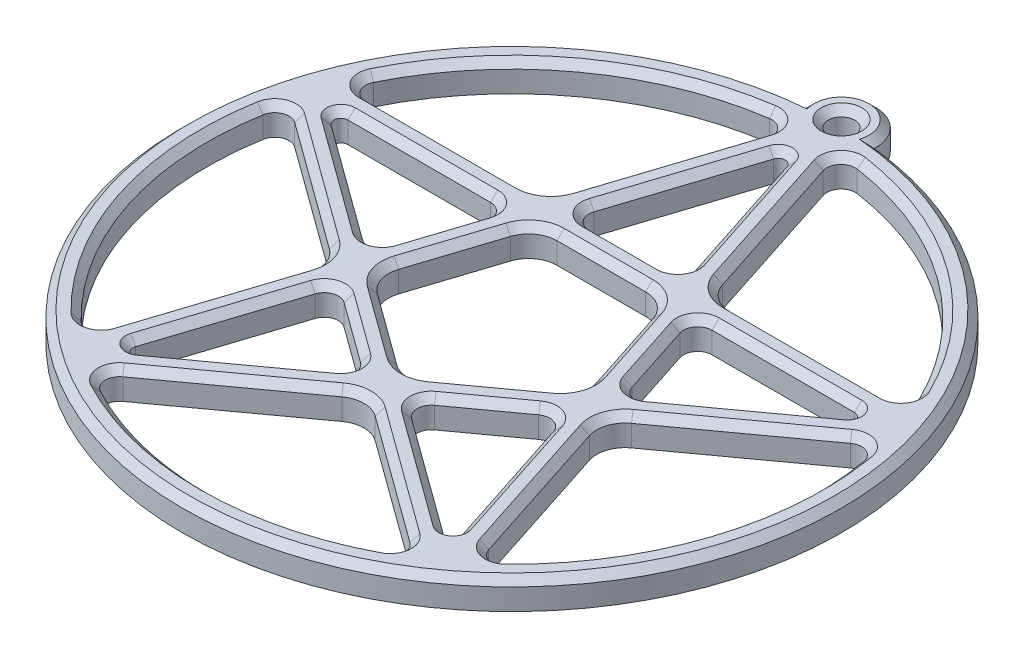
SolidWorks part; units mm, degrees
ref_plane "Front Plane" through (0, 0, 0) normal (0, 0, 1) x (1, 0, 0)
ref_plane "Top Plane" through (0, 0, 0) normal (0, 1, 0) x (1, 0, 0)
ref_plane "Right Plane" through (0, 0, 0) normal (1, 0, 0) x (0, 0, -1)
sketch "Sketch1" plane through (0, 0, 0) normal (0, 1, 0) x (1, 0, 0)
  line L0 (-44.0839, 14.3237) -> (44.0839, 14.3237) construction
  line L1 (44.0839, 14.3237) -> (0, 46.3525) construction
  line L2 (0, 46.3525) -> (-44.0839, 14.3237) construction
  line L3 (-44.0839, 14.3237) -> (-27.2453, -37.5) construction
  line L4 (-27.2453, -37.5) -> (27.2453, -37.5) construction
  line L5 (27.2453, -37.5) -> (44.0839, 14.3237) construction
  line L6 (44.0839, 14.3237) -> (-27.2453, -37.5) construction
  line L7 (-27.2453, -37.5) -> (0, 46.3525) construction
  line L8 (0, 46.3525) -> (27.2453, -37.5) construction
  line L9 (27.2453, -37.5) -> (-44.0839, 14.3237) construction
  line L10 (-43.4764, 16.0737) -> (43.4764, 16.0737) construction
  line L11 (-44.6146, 12.5737) -> (44.6146, 12.5737) construction
  line L12 (-1.8521, 46.3155) -> (-28.722, -36.3814) construction
  line L13 (1.8283, 46.3165) -> (-25.745, -38.5455) construction
  line L14 (-1.8283, 46.3165) -> (25.745, -38.5455) construction
  line L15 (1.8521, 46.3155) -> (28.722, -36.3814) construction
  line L16 (-43.4846, 16.0514) -> (28.7033, -36.3961) construction
  line L17 (-44.621, 12.5508) -> (25.7252, -38.5587) construction
  line L18 (-28.7033, -36.3961) -> (43.4846, 16.0514) construction
  line L19 (-10.0334, 9.8098) -> (-13.8832, -2.0388)
  line L20 (-25.7252, -38.5587) -> (44.621, 12.5508) construction
  line L21 (-12.4302, -6.5109) -> (-2.3511, -13.8338)
  line L22 (2.3511, -13.8338) -> (12.4302, -6.5109)
  line L23 (13.8832, -2.0388) -> (10.0334, 9.8098)
  line L24 (6.2292, 12.5737) -> (-6.2292, 12.5737)
  line L25 (39.0879, 8.5308) -> (21.2469, -4.4314)
  line L26 (19.7939, -8.9035) -> (26.6085, -29.8768)
  line L27 (36.637, 16.0737) -> (14.5844, 16.0737)
  line L28 (10.7802, 18.8377) -> (3.9656, 39.8109)
  line L29 (-3.9656, 39.8109) -> (-10.7802, 18.8377)
  line L30 (-14.5844, 16.0737) -> (-36.637, 16.0737)
  line L31 (-39.0879, 8.5308) -> (-21.2469, -4.4314)
  line L32 (-19.7939, -8.9035) -> (-26.6085, -29.8768)
  line L33 (-20.1921, -34.5386) -> (-2.3511, -21.5764)
  line L34 (2.3511, -21.5764) -> (20.1921, -34.5386)
  line L35 (-15.5682, 12.5737) -> (-35.6203, 12.5737)
  line L36 (-36.208, 10.7647) -> (-19.9856, -1.0216)
  line L37 (-16.9079, -0.0216) -> (-13.6661, 9.9557)
  line L38 (-7.1475, 18.6918) -> (-0.9511, 37.7624)
  line L39 (0.9511, 37.7624) -> (7.1475, 18.6918)
  line L40 (5.2454, 16.0737) -> (-5.2454, 16.0737)
  line L41 (15.5682, 12.5737) -> (35.6203, 12.5737)
  line L42 (36.208, 10.7647) -> (19.9856, -1.0216)
  line L43 (16.9079, -0.0216) -> (13.6661, 9.9557)
  line L44 (22.9656, -29.9914) -> (16.7692, -10.9208)
  line L45 (13.6915, -9.9208) -> (5.2043, -16.0871)
  line L46 (5.2043, -19.3231) -> (21.4267, -31.1094)
  line L47 (-22.9656, -29.9914) -> (-16.7692, -10.9208)
  line L48 (-13.6915, -9.9208) -> (-5.2043, -16.0871)
  line L49 (-5.2043, -19.3231) -> (-21.4267, -31.1094)
  circle A0 centre (0, 0) radius 37.5 construction
  circle A1 centre (0, 0) radius 46.3525 construction
  circle A2 centre (0, 0) radius 42.8525 construction
  arc A3 (-13.8832, -2.0388) -> (-12.4302, -6.5109) centre (-10.079, -3.2749) ccw
  arc A4 (-2.3511, -13.8338) -> (2.3511, -13.8338) centre (0, -10.5977) ccw
  arc A5 (12.4302, -6.5109) -> (13.8832, -2.0388) centre (10.079, -3.2749) ccw
  arc A6 (10.0334, 9.8098) -> (6.2292, 12.5737) centre (6.2292, 8.5737) ccw
  arc A7 (-10.0334, 9.8098) -> (-6.2292, 12.5737) centre (-6.2292, 8.5737) cw
  arc A8 (-29.9064, -30.6912) -> (-42.2346, 7.2512) centre (0, 0) cw
  arc A9 (-38.4306, 18.9586) -> (-6.1549, 42.4082) centre (0, 0) cw
  arc A10 (6.1549, 42.4082) -> (38.4306, 18.9586) centre (0, 0) cw
  arc A11 (42.2346, 7.2512) -> (29.9064, -30.6912) centre (0, 0) cw
  arc A12 (19.9475, -37.9268) -> (-19.9475, -37.9268) centre (0, 0) cw
  arc A13 (-10.7802, 18.8377) -> (-14.5844, 16.0737) centre (-14.5844, 20.0737) cw
  arc A14 (14.5844, 16.0737) -> (10.7802, 18.8377) centre (14.5844, 20.0737) cw
  arc A15 (21.2469, -4.4314) -> (19.7939, -8.9035) centre (23.5981, -7.6675) ccw
  arc A16 (-2.3511, -21.5764) -> (2.3511, -21.5764) centre (0, -24.8125) cw
  arc A17 (-21.2469, -4.4314) -> (-19.7939, -8.9035) centre (-23.5981, -7.6675) cw
  arc A18 (-38.4306, 18.9586) -> (-36.637, 16.0737) centre (-36.637, 18.0737) ccw
  arc A19 (-42.2346, 7.2512) -> (-39.0879, 8.5308) centre (-40.2634, 6.9127) cw
  arc A20 (-29.9064, -30.6912) -> (-26.6085, -29.8768) centre (-28.5106, -29.2588) ccw
  arc A21 (-19.9475, -37.9268) -> (-20.1921, -34.5386) centre (-19.0165, -36.1567) cw
  arc A22 (19.9475, -37.9268) -> (20.1921, -34.5386) centre (19.0165, -36.1567) ccw
  arc A23 (29.9064, -30.6912) -> (26.6085, -29.8768) centre (28.5106, -29.2588) cw
  arc A24 (42.2346, 7.2512) -> (39.0879, 8.5308) centre (40.2634, 6.9127) ccw
  arc A25 (38.4306, 18.9586) -> (36.637, 16.0737) centre (36.637, 18.0737) cw
  arc A26 (6.1549, 42.4082) -> (3.9656, 39.8109) centre (5.8677, 40.429) ccw
  arc A27 (-6.1549, 42.4082) -> (-3.9656, 39.8109) centre (-5.8677, 40.429) cw
  arc A28 (-19.9856, -1.0216) -> (-16.9079, -0.0216) centre (-18.81, 0.5965) ccw
  arc A29 (-15.5682, 12.5737) -> (-13.6661, 9.9557) centre (-15.5682, 10.5737) cw
  arc A30 (-7.1475, 18.6918) -> (-5.2454, 16.0737) centre (-5.2454, 18.0737) ccw
  arc A31 (7.1475, 18.6918) -> (5.2454, 16.0737) centre (5.2454, 18.0737) cw
  arc A32 (15.5682, 12.5737) -> (13.6661, 9.9557) centre (15.5682, 10.5737) ccw
  arc A33 (19.9856, -1.0216) -> (16.9079, -0.0216) centre (18.81, 0.5965) cw
  arc A34 (16.7692, -10.9208) -> (13.6915, -9.9208) centre (14.8671, -11.5388) ccw
  arc A35 (5.2043, -16.0871) -> (5.2043, -19.3231) centre (6.3799, -17.7051) ccw
  arc A36 (-5.2043, -16.0871) -> (-5.2043, -19.3231) centre (-6.3799, -17.7051) cw
  arc A37 (-16.7692, -10.9208) -> (-13.6915, -9.9208) centre (-14.8671, -11.5388) cw
  arc A38 (-22.9656, -29.9914) -> (-21.4267, -31.1094) centre (-22.0145, -30.3004) ccw
  arc A39 (22.9656, -29.9914) -> (21.4267, -31.1094) centre (22.0145, -30.3004) cw
  arc A40 (35.6203, 12.5737) -> (36.208, 10.7647) centre (35.6203, 11.5737) cw
  arc A41 (-0.9511, 37.7624) -> (0.9511, 37.7624) centre (0, 37.4534) cw
  arc A42 (-35.6203, 12.5737) -> (-36.208, 10.7647) centre (-35.6203, 11.5737) ccw
  circle A43 centre (0, 46.3525) radius 1.8525
  arc A44 (-4.8458, 46.0986) -> (4.8458, 46.0986) centre (0, 46.3525) cw
  arc A45 (-4.8458, 46.0986) -> (4.8458, 46.0986) centre (0, 0) ccw
  point P37 (-14.7813, -4.8027)
  point P40 (0, -15.542)
  point P43 (14.7813, -4.8027)
  point P46 (9.1353, 12.5737)
  point P49 (-9.1353, 12.5737)
  point P67 (-11.6782, 16.0737)
  point P70 (11.6782, 16.0737)
  point P73 (18.8958, -6.1396)
  point P76 (0, -19.8682)
  point P79 (-18.8958, -6.1396)
  point P82 (-39.7238, 16.0737)
  point P85 (-41.5851, 10.3451)
  point P88 (-27.5623, -32.8125)
  point P91 (-22.6893, -36.353)
  point P94 (22.6893, -36.353)
  point P97 (27.5623, -32.8125)
  point P100 (41.5851, 10.3451)
  point P103 (39.7238, 16.0737)
  point P106 (3.0117, 42.7466)
  point P109 (-3.0117, 42.7466)
  point P127 (-17.7586, -2.6396)
  point P130 (-12.8155, 12.5737)
  point P133 (-7.9981, 16.0737)
  point P136 (7.9981, 16.0737)
  point P139 (12.8155, 12.5737)
  point P142 (17.7586, -2.6396)
  point P145 (15.9185, -8.3027)
  point P148 (2.9773, -17.7051)
  point P151 (-2.9773, -17.7051)
  point P154 (-15.9185, -8.3027)
  point P157 (-23.9166, -32.9184)
  point P160 (23.9166, -32.9184)
  point P163 (38.6979, 12.5737)
  point P166 (0, 40.6894)
  point P169 (-38.6979, 12.5737)
  dimension "D1" = 75
  dimension "D2" = 3.5
  dimension "D13" = 4
  dimension "D14" = 4
  dimension "D15" = 2
  dimension "D16" = 2
  dimension "D17" = 1
  dimension "D18" = 3
  dimension "D3" = 1.75
  dimension "D4" = 1.75
  dimension "D5" = 1.75
  dimension "D6" = 1.75
  dimension "D7" = 1.75
  dimension "D8" = 1.75
  dimension "D9" = 1.75
  dimension "D10" = 1.75
  dimension "D11" = 1.75
  dimension "D12" = 1.75
extrude "Boss-Extrude1" add sketch "Sketch1" along normal blind 4
chamfer "Chamfer1" distance 1 angle 45 73 edges at (18.192, 4, 1.3057) (28.0968, 4, -4.8716) (15.287, 4, -4.9671) (36.5713, 4, -11.8827) (13.9502, 4, -11.7493) (25.5942, 4, -12.5737) (28.0311, 4, 31.2005) (40.7552, 4, 13.2422) (23.2012, 4, 19.3902) (41.0168, 4, -8.7654) (19.7939, 4, 6.4314) (30.1674, 4, -2.0497) (22.6023, 4, 31.1094) (19.8674, 4, 20.4561) (13.3155, 4, 25.2163) (15.4851, 4, 9.6367) (4.3799, 4, 17.7051) (9.4479, 4, 13.0039) (0, 4, 42.8525) (21.0113, 4, 36.3007) (-21.0113, 4, 36.3007) (11.2716, 4, 28.0575) (-11.2716, 4, 28.0575) (0, 4, 20.8125) (-22.6023, 4, 31.1094) (-13.3155, 4, 25.2163) (-19.8674, 4, 20.4561) (-4.3799, 4, 17.7051) (-15.4851, 4, 9.6367) (-9.4479, 4, 13.0039) (-28.0311, 4, 31.2005) (-23.2012, 4, 19.3902) (-40.7552, 4, 13.2422) (-19.7939, 4, 6.4314) (-41.0168, 4, -8.7654) (-30.1674, 4, -2.0497) (-18.192, 4, 1.3057) (-15.287, 4, -4.9671) (-28.0968, 4, -4.8716) (-13.9502, 4, -11.7493) (-36.5713, 4, -11.8827) (-25.5942, 4, -12.5737) (-38.3355, 4, -17.0177) (-25.6107, 4, -16.0737) (-25.1881, 4, -34.6684) (-12.2333, 4, -16.8377) (-4.3385, 4, -41.718) (-7.3729, 4, -29.3243) (38.3355, 4, -17.0177) (25.1881, 4, -34.6684) (25.6107, 4, -16.0737) (4.3385, 4, -41.718) (12.2333, 4, -16.8377) (7.3729, 4, -29.3243) (-6.8634, 4, -16.8982) (0, 4, -16.0737) (-4.0493, 4, -28.2271) (6.8634, 4, -16.8982) (0, 4, -38.4534) (4.0493, 4, -28.2271) (0, 4, 14.5977) (7.3907, 4, 10.1724) (-7.3907, 4, 10.1724) (13.8832, 4, 4.5109) (-13.8832, 4, 4.5109) (11.9583, 4, -3.8855) (-11.9583, 4, -3.8855) (8.5803, 4, -11.8098) (-8.5803, 4, -11.8098) (0, 4, -12.5737) (0, 4, -44.5001) (0, 4, -51.205) (0, 4, 46.3525)
